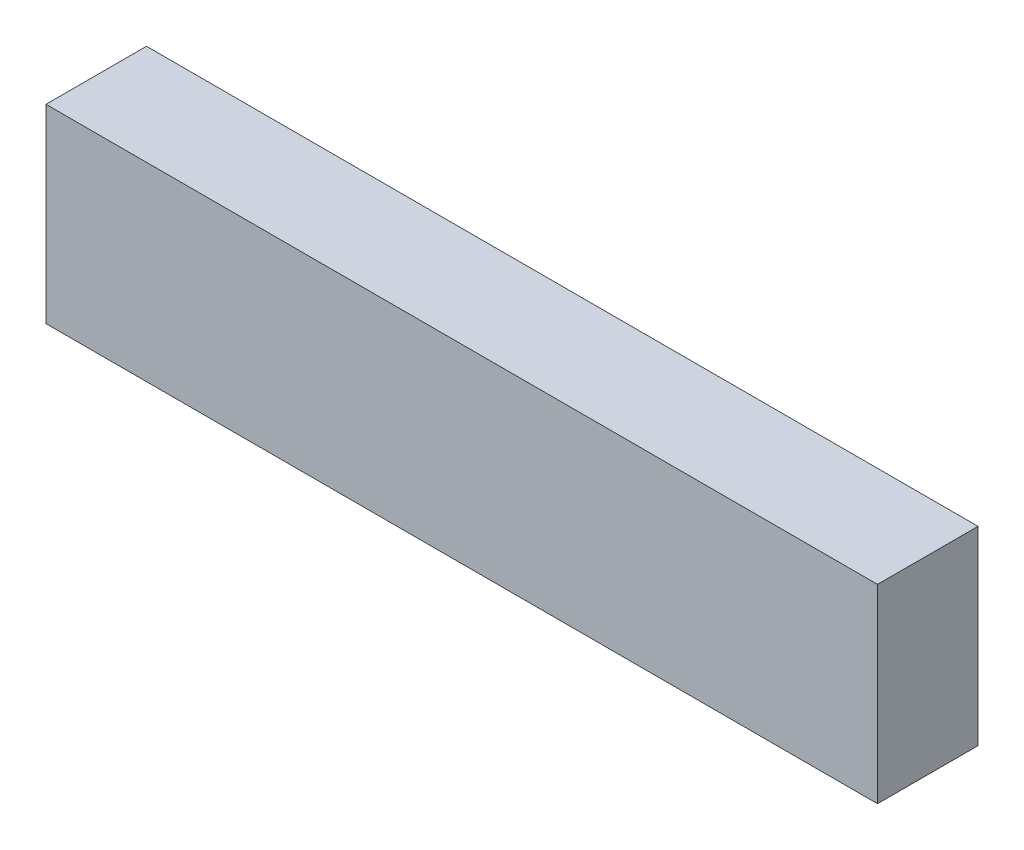
SolidWorks part; units mm, degrees
ref_plane "Спереди" through (0, 0, 0) normal (0, 0, 1) x (1, 0, 0)
ref_plane "Сверху" through (0, 0, 0) normal (0, 1, 0) x (1, 0, 0)
ref_plane "Справа" through (0, 0, 0) normal (1, 0, 0) x (0, 0, -1)
other "Configuration Table"
sketch "Эскиз1" plane through (0, 0, 0) normal (0, 0, 1) x (1, 0, 0)
  line L1 (-30.2, 6.9) -> (30.2, 6.9)
  line L2 (-30.2, 6.9) -> (-30.2, -6.9)
  line L3 (-30.2, -6.9) -> (30.2, -6.9)
  line L4 (30.2, 6.9) -> (30.2, -6.9)
  dimension "D1" = 60.4
  dimension "D2" = 13.8
  dimension "D3" = 30.2
  dimension "D4" = 6.9
extrude "Бобышка-Вытянуть1" add sketch "Эскиз1" along normal blind 7.3
